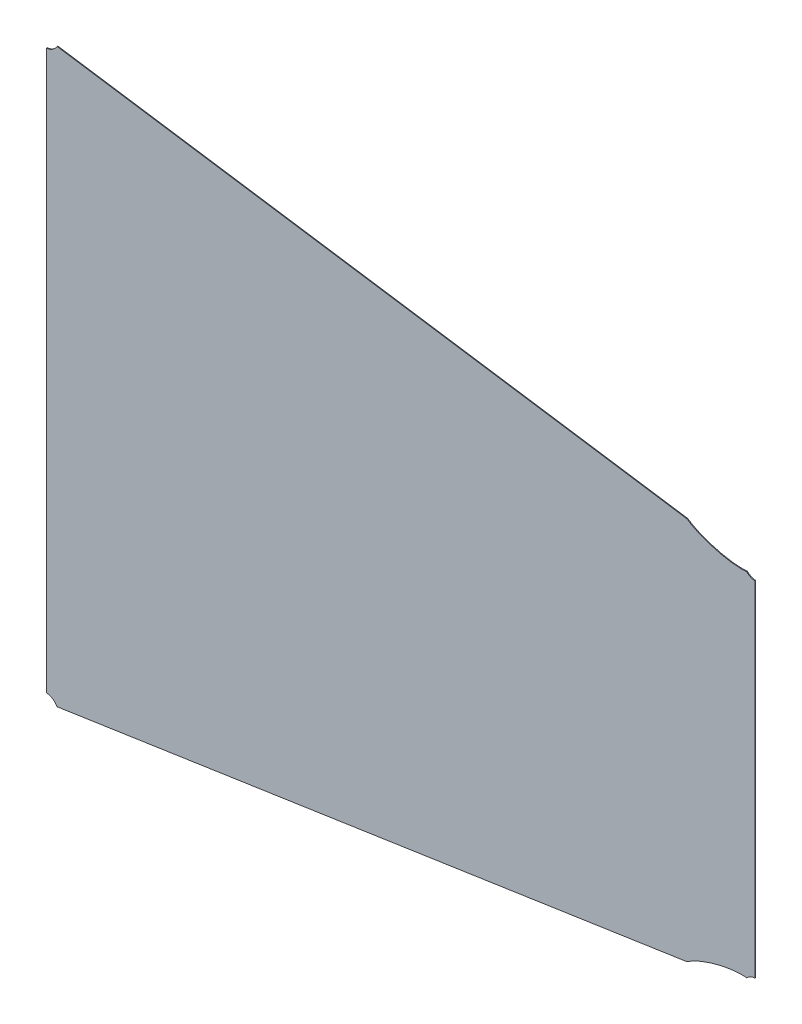
SolidWorks part; units mm, degrees
material "Hexcel AS4C (3000 Filamentów)"
ref_plane "Front Plane" through (0, 0, 0) normal (0, 0, 1) x (1, 0, 0)
ref_plane "Top Plane" through (0, 0, 0) normal (0, 1, 0) x (1, 0, 0)
ref_plane "Right Plane" through (0, 0, 0) normal (1, 0, 0) x (0, 0, -1)
sketch "Szkic2" plane through (0, 0, 0) normal (0, 0, 1) x (1, 0, 0)
  line L0 (-197.1801, -175.2824) -> (-197.1801, 175.2824)
  line L1 (-266.7378, 195.4035) -> (-906.194, 290.9985)
  line L2 (-917.4239, 284.0896) -> (-917.4239, -284.0896)
  line L3 (-906.194, -290.9985) -> (-266.7378, -195.4035)
  line L8 (-198.1801, -174.3434) -> (-198.1801, 174.3434)
  line L9 (-267.1164, 194.449) -> (-905.6574, 289.9071)
  line L10 (-916.4239, 283.1113) -> (-916.4239, -283.1113)
  line L11 (-905.6574, -289.9071) -> (-267.1164, -194.449)
  spline S0 degree 1 poles (-267.1164, -194.449) (-206.3506, -178.2343) knots 0 0 1 1 construction
  spline S1 degree 1 poles (-206.3506, -178.2343) (-198.1801, -174.3434) knots 0 0 1 1 construction
  spline S3 degree 3 poles (-197.1801, 175.2824) (-197.7708, 175.2975) (-198.3467, 175.3546) (-198.9047, 175.4482) (-201.4053, 175.8674) (-203.9269, 177.0674) (-205.9635, 179.2757) knots 0.967523 0.967523 0.967523 0.967523 1 1 1 1.126478 1.126478 1.126478 1.126478 weights 0.878532 0.916208 0.956698 1 0.831362 0.705382 0.622061
  spline S5 degree 3 poles (-205.9635, 179.2757) (-223.1781, 177.5334) (-250.1061, 183.7934) (-266.7378, 195.4035) knots 0 0 0 0 0.35695 0.35695 0.35695 0.35695 weights 1 0.699143 0.613068 0.741774
  spline S7 degree 3 poles (-906.194, 290.9985) (-908.7806, 286.0773) (-913.2125, 284.0092) (-917.4239, 284.0896) knots 0.305598 0.305598 0.305598 0.305598 0.487901 0.487901 0.487901 0.487901 weights 0.524729 0.578787 0.721468 0.952775
  spline S9 degree 3 poles (-917.4239, -284.0896) (-913.2125, -284.0092) (-908.7806, -286.0773) (-906.194, -290.9985) knots 0.012099 0.012099 0.012099 0.012099 0.194402 0.194402 0.194402 0.194402 weights 0.952775 0.721468 0.578787 0.524729
  spline S11 degree 3 poles (-266.7378, -195.4035) (-250.1061, -183.7934) (-223.1781, -177.5334) (-205.9635, -179.2757) knots 0.64305 0.64305 0.64305 0.64305 1 1 1 1 weights 0.741774 0.613068 0.699143 1
  spline S12 degree 3 poles (-205.9635, -179.2757) (-203.9269, -177.0674) (-201.4053, -175.8674) (-198.9047, -175.4482) (-198.3467, -175.3546) (-197.7708, -175.2975) (-197.1801, -175.2824) knots 0.373522 0.373522 0.373522 0.373522 0.5 0.5 0.5 0.532477 0.532477 0.532477 0.532477 weights 0.622061 0.705382 0.831362 1 0.956698 0.916208 0.878532
  spline S13 degree 1 poles (-198.1801, 174.3434) (-206.3506, 178.2343) knots 0 0 1 1 construction
  spline S14 degree 1 poles (-206.3506, 178.2343) (-267.1164, 194.449) knots 0 0 1 1 construction
  spline S15 degree 1 poles (-905.6574, 289.9071) (-916.4239, 283.1113) knots 0 0 1 1 construction
  spline S16 degree 1 poles (-916.4239, -283.1113) (-905.6574, -289.9071) knots 0 0 1 1 construction
  spline S17 degree 3 poles (-267.1164, -194.449) (-266.6651, -194.1375) (-265.7719, -193.5436) (-263.7832, -192.31) (-261.0349, -190.7686) (-257.3171, -188.9303) (-251.8897, -186.5535) (-244.401, -183.8159) (-235.0415, -181.1746) (-226.0832, -179.3275) (-219.4423, -178.459) (-214.7789, -178.117) (-211.6154, -178.0186) (-209.2668, -178.0515) (-207.5399, -178.1386) (-206.753, -178.1983) (-206.3506, -178.2343) knots 0.644679 0.644679 0.644679 0.644679 0.655638 0.666597 0.688514 0.710432 0.73235 0.776185 0.82002 0.863855 0.907691 0.929608 0.951526 0.973444 0.984402 0.995361 0.995361 0.995361 0.995361
  spline S18 degree 3 poles (-206.3506, -178.2343) (-206.0169, -177.8984) (-205.2972, -177.249) (-203.8614, -176.2037) (-202.0571, -175.26) (-200.0294, -174.6105) (-198.814, -174.4062) (-198.1801, -174.3434) knots 0.379344 0.379344 0.379344 0.379344 0.396436 0.413529 0.447714 0.481899 0.516084 0.516084 0.516084 0.516084
  spline S19 degree 3 poles (-198.1801, 174.3434) (-198.814, 174.4062) (-200.0294, 174.6105) (-202.0571, 175.26) (-203.8614, 176.2037) (-205.2972, 177.249) (-206.0169, 177.8984) (-206.3506, 178.2343) knots 0.983916 0.983916 0.983916 0.983916 1.018101 1.052286 1.086471 1.103564 1.120656 1.120656 1.120656 1.120656
  spline S20 degree 3 poles (-206.3506, 178.2343) (-206.753, 178.1983) (-207.5399, 178.1386) (-209.2668, 178.0515) (-211.6154, 178.0186) (-214.7789, 178.117) (-219.4423, 178.459) (-226.0832, 179.3275) (-235.0415, 181.1746) (-244.401, 183.8159) (-251.8897, 186.5535) (-257.3171, 188.9303) (-261.0349, 190.7686) (-263.7832, 192.31) (-265.7719, 193.5436) (-266.6651, 194.1375) (-267.1164, 194.449) knots 0.004639 0.004639 0.004639 0.004639 0.015598 0.026556 0.048474 0.070392 0.092309 0.136145 0.17998 0.223815 0.26765 0.289568 0.311486 0.333403 0.344362 0.355321 0.355321 0.355321 0.355321
  spline S21 degree 3 poles (-905.6574, 289.9071) (-906.0061, 289.3152) (-906.8046, 288.1593) (-908.5725, 286.2492) (-911.0156, 284.5221) (-913.4044, 283.6036) (-915.1943, 283.225) (-916.0053, 283.137) (-916.4239, 283.1113) knots 0.312268 0.312268 0.312268 0.312268 0.332062 0.351857 0.391446 0.431035 0.450829 0.470624 0.470624 0.470624 0.470624
  spline S22 degree 3 poles (-916.4239, -283.1113) (-916.0053, -283.137) (-915.1943, -283.225) (-913.4044, -283.6036) (-911.0156, -284.5221) (-908.5725, -286.2492) (-906.8046, -288.1593) (-906.0061, -289.3152) (-905.6574, -289.9071) knots 0.029376 0.029376 0.029376 0.029376 0.049171 0.068965 0.108554 0.148143 0.167938 0.187732 0.187732 0.187732 0.187732
  dimension "D1" = 1
extrude "Dodanie-wyciągnięcie1" add sketch "Szkic2" along normal blind 0.75 contours L9 S21 L10 S22 L11 S17 S18 L8 S19 S20
